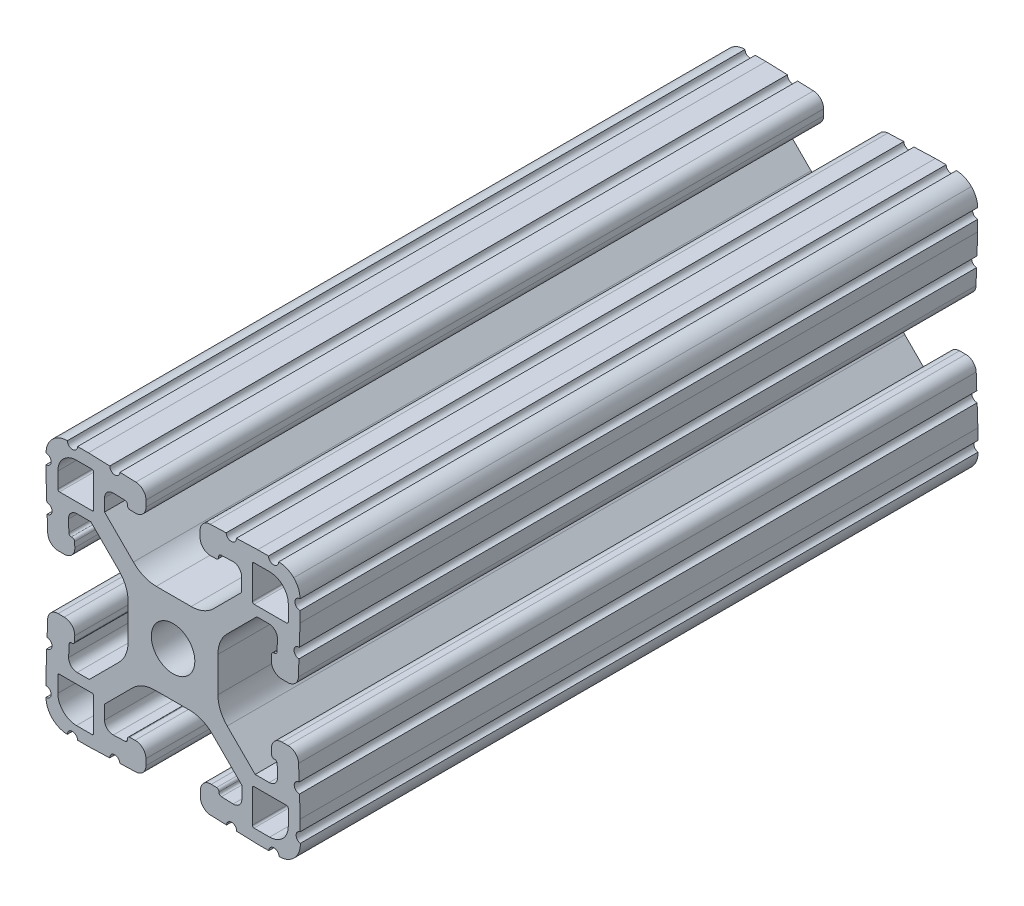
SolidWorks part; units mm, degrees
material "6061-T6 (SS)"
ref_plane "Front Plane" through (0, 0, 0) normal (0, 0, 1) x (1, 0, 0)
ref_plane "Top Plane" through (0, 0, 0) normal (0, 1, 0) x (1, 0, 0)
ref_plane "Right Plane" through (0, 0, 0) normal (1, 0, 0) x (0, 0, -1)
ref_plane "Plane1" through (0, 0, -25.4) normal (0, 0, -1) x (-1, 0, 0)
sketch "Sketch1" plane through (0, 0, -25.4) normal (0, 0, -1) x (-1, 0, 0)
  line L0 (-83.3577, 88.2941) -> (-83.3577, 93.1709)
  line L1 (-83.1037, 93.4249) -> (-80.767, 93.4249)
  line L2 (-77.9729, 90.6309) -> (-77.9729, 88.2941)
  line L3 (-78.2269, 88.0401) -> (-83.1037, 88.0401)
  line L4 (-83.3577, 59.2291) -> (-83.3577, 64.1059)
  line L5 (-83.1037, 64.3599) -> (-78.2269, 64.3599)
  line L6 (-77.9729, 64.1059) -> (-77.9729, 61.7691)
  line L7 (-80.767, 58.9751) -> (-83.1037, 58.9751)
  line L8 (-107.1423, 93.1709) -> (-107.1423, 88.2941)
  line L9 (-107.3963, 88.0401) -> (-112.2731, 88.0401)
  line L10 (-112.5271, 88.2941) -> (-112.5271, 90.6309)
  line L11 (-109.733, 93.4249) -> (-107.3963, 93.4249)
  line L12 (-107.1423, 64.1059) -> (-107.1423, 59.2291)
  line L13 (-107.3963, 58.9751) -> (-109.733, 58.9751)
  line L14 (-112.5271, 61.7691) -> (-112.5271, 64.1059)
  line L15 (-112.2731, 64.3599) -> (-107.3963, 64.3599)
  line L16 (-88.0437, 91.8626) -> (-86.2967, 91.9236)
  line L17 (-84.9824, 90.6544) -> (-84.9824, 88.8002)
  line L18 (-84.9824, 88.8002) -> (-89.3066, 84.476)
  line L19 (-92.7196, 83.0295) -> (-97.9616, 83.0295)
  line L20 (-101.3202, 84.4207) -> (-105.516, 88.6165)
  line L21 (-105.516, 88.6165) -> (-105.516, 90.7313)
  line L22 (-104.2017, 92.0006) -> (-102.4547, 91.9396)
  line L23 (-101.7262, 91.1059) -> (-100.9297, 91.0781)
  line L24 (-99.2999, 92.6519) -> (-99.2999, 93.5668)
  line L25 (-100.8197, 95.1407) -> (-103.2119, 95.2242)
  line L26 (-104.735, 95.2774) -> (-107.9359, 95.3892)
  line L27 (-107.9359, 95.3892) -> (-109.5615, 95.3892)
  line L28 (-114.2859, 90.6648) -> (-114.2859, 89.0392)
  line L29 (-114.2859, 89.0392) -> (-114.1741, 85.8383)
  line L30 (-114.1209, 84.3152) -> (-114.0374, 81.9231)
  line L31 (-112.4635, 80.4032) -> (-111.5486, 80.4032)
  line L32 (-109.9748, 82.033) -> (-110.0026, 82.8295)
  line L33 (-110.8377, 83.5577) -> (-110.8987, 85.3047)
  line L34 (-109.6294, 86.619) -> (-107.8072, 86.619)
  line L35 (-107.8072, 86.619) -> (-103.3649, 82.1768)
  line L36 (-101.9737, 78.8182) -> (-101.9737, 73.576)
  line L37 (-103.3649, 70.2174) -> (-107.5607, 66.0217)
  line L38 (-107.5607, 66.0217) -> (-109.6524, 66.0217)
  line L39 (-110.9217, 67.336) -> (-110.8607, 69.083)
  line L40 (-110.0322, 69.8124) -> (-110.0043, 70.6089)
  line L41 (-111.5782, 72.2387) -> (-112.4931, 72.2387)
  line L42 (-114.0669, 70.7189) -> (-114.1505, 68.3267)
  line L43 (-114.2036, 66.8036) -> (-114.3154, 63.6027)
  line L44 (-114.3154, 63.6027) -> (-114.3154, 61.9626)
  line L45 (-109.6111, 57.1437) -> (-107.9855, 57.1437)
  line L46 (-107.9855, 57.1437) -> (-104.7846, 57.2555)
  line L47 (-103.2615, 57.3086) -> (-100.8694, 57.3922)
  line L48 (-99.3495, 58.966) -> (-99.3495, 59.8809)
  line L49 (-100.9794, 61.4548) -> (-101.7758, 61.4269)
  line L50 (-102.5054, 60.599) -> (-104.2524, 60.538)
  line L51 (-105.5667, 61.8072) -> (-105.5667, 63.6295)
  line L52 (-105.5667, 63.6295) -> (-101.1311, 68.065)
  line L53 (-97.7725, 69.4562) -> (-92.5304, 69.4562)
  line L54 (-89.1717, 68.065) -> (-84.976, 63.8692)
  line L55 (-84.976, 63.8692) -> (-84.976, 61.7811)
  line L56 (-86.2903, 60.5118) -> (-88.0373, 60.5728)
  line L57 (-88.7596, 61.4332) -> (-89.5561, 61.461)
  line L58 (-91.1859, 59.8872) -> (-91.1859, 58.9723)
  line L59 (-89.6661, 57.3985) -> (-87.2739, 57.3149)
  line L60 (-85.7508, 57.2617) -> (-82.5499, 57.15)
  line L61 (-82.5499, 57.15) -> (-80.9244, 57.15)
  line L62 (-76.2, 61.8744) -> (-76.2, 63.4999)
  line L63 (-76.2, 63.4999) -> (-76.3117, 66.7008)
  line L64 (-76.3649, 68.2239) -> (-76.4484, 70.6161)
  line L65 (-78.0223, 72.1359) -> (-78.9372, 72.1359)
  line L66 (-80.511, 70.5061) -> (-80.4832, 69.7096)
  line L67 (-79.6552, 68.9801) -> (-79.5942, 67.2331)
  line L68 (-80.8634, 65.9188) -> (-82.6857, 65.9188)
  line L69 (-82.6857, 65.9188) -> (-87.1213, 70.3543)
  line L70 (-88.5125, 73.7128) -> (-88.5126, 78.955)
  line L71 (-87.1214, 82.3137) -> (-82.9257, 86.5095)
  line L72 (-82.9257, 86.5095) -> (-80.8375, 86.5095)
  line L73 (-79.5682, 85.1951) -> (-79.6293, 83.4482)
  line L74 (-80.4896, 82.7258) -> (-80.5175, 81.9294)
  line L75 (-78.9436, 80.2995) -> (-78.0287, 80.2995)
  line L76 (-76.4549, 81.8194) -> (-76.3713, 84.2115)
  line L77 (-76.3182, 85.7346) -> (-76.2064, 88.9355)
  line L78 (-76.2064, 88.9355) -> (-76.2064, 90.5611)
  line L79 (-80.9308, 95.2855) -> (-82.5564, 95.2855)
  line L80 (-82.5564, 95.2855) -> (-85.7573, 95.1737)
  line L81 (-87.2803, 95.1205) -> (-89.6725, 95.037)
  line L82 (-91.1924, 93.4632) -> (-91.1924, 92.5483)
  line L83 (-89.5625, 90.9744) -> (-88.7661, 91.0023)
  arc A0 (-83.3577, 93.1709) -> (-83.1037, 93.4249) centre (-83.1037, 93.1709) cw
  arc A1 (-80.767, 93.4249) -> (-77.9729, 90.6309) centre (-80.7669, 90.6309) cw
  arc A2 (-77.9729, 88.2941) -> (-78.2269, 88.0401) centre (-78.2269, 88.2941) cw
  arc A3 (-83.1037, 88.0401) -> (-83.3577, 88.2941) centre (-83.1037, 88.2941) cw
  arc A4 (-83.1037, 58.9751) -> (-83.3577, 59.2291) centre (-83.1037, 59.2291) cw
  arc A5 (-83.3577, 64.1059) -> (-83.1037, 64.3599) centre (-83.1037, 64.1059) cw
  arc A6 (-78.2269, 64.3599) -> (-77.9729, 64.1059) centre (-78.2269, 64.1059) cw
  arc A7 (-77.9729, 61.7691) -> (-80.767, 58.9751) centre (-80.7669, 61.7691) cw
  arc A8 (-107.3963, 93.4249) -> (-107.1423, 93.1709) centre (-107.3963, 93.1709) cw
  arc A9 (-107.1423, 88.2941) -> (-107.3963, 88.0401) centre (-107.3963, 88.2941) cw
  arc A10 (-112.2731, 88.0401) -> (-112.5271, 88.2941) centre (-112.2731, 88.2941) cw
  arc A11 (-112.5271, 90.6309) -> (-109.733, 93.4249) centre (-109.7331, 90.6309) cw
  arc A12 (-107.1423, 59.2291) -> (-107.3963, 58.9751) centre (-107.3963, 59.2291) cw
  arc A13 (-109.733, 58.9751) -> (-112.5271, 61.7691) centre (-109.7331, 61.7691) cw
  arc A14 (-112.5271, 64.1059) -> (-112.2731, 64.3599) centre (-112.2731, 64.1059) cw
  arc A15 (-107.3963, 64.3599) -> (-107.1423, 64.1059) centre (-107.3963, 64.1059) cw
  circle A16 centre (-95.25, 76.2) radius 3.2639
  arc A17 (-88.7661, 91.0023) -> (-88.3984, 91.383) centre (-88.7794, 91.383) ccw
  arc A18 (-88.3984, 91.383) -> (-88.0437, 91.8626) centre (-88.0304, 91.4819) cw
  arc A19 (-86.2967, 91.9236) -> (-84.9824, 90.6544) centre (-86.2524, 90.6544) cw
  arc A20 (-89.3066, 84.476) -> (-92.7196, 83.0295) centre (-92.7196, 87.7793) cw
  arc A21 (-97.9616, 83.0295) -> (-101.3202, 84.4207) centre (-97.9616, 87.7793) cw
  arc A22 (-105.516, 90.7313) -> (-104.2017, 92.0006) centre (-104.246, 90.7313) cw
  arc A23 (-102.4547, 91.9396) -> (-102.087, 91.5588) centre (-102.468, 91.5588) cw
  arc A24 (-102.087, 91.5588) -> (-101.7262, 91.1059) centre (-101.7129, 91.4867) ccw
  arc A25 (-100.9297, 91.0781) -> (-99.2999, 92.6519) centre (-100.8747, 92.6519) ccw
  arc A26 (-99.2999, 93.5668) -> (-100.8197, 95.1407) centre (-100.8747, 93.5668) ccw
  arc A27 (-103.2119, 95.2242) -> (-104.735, 95.2774) centre (-103.9735, 95.2508) cw
  arc A28 (-109.5615, 95.3892) -> (-111.0855, 95.3892) centre (-110.3235, 95.3892) cw
  arc A29 (-111.0855, 95.3892) -> (-113.3432, 94.4465) centre (-111.0855, 92.2142) ccw
  arc A30 (-113.3432, 94.4465) -> (-114.2859, 92.1888) centre (-111.1109, 92.1888) ccw
  arc A31 (-114.2859, 92.1888) -> (-114.2859, 90.6648) centre (-114.2859, 91.4268) cw
  arc A32 (-114.1741, 85.8383) -> (-114.1209, 84.3152) centre (-114.1475, 85.0768) cw
  arc A33 (-114.0374, 81.9231) -> (-112.4635, 80.4032) centre (-112.4635, 81.978) ccw
  arc A34 (-111.5486, 80.4032) -> (-109.9748, 82.033) centre (-111.5486, 81.978) ccw
  arc A35 (-110.0026, 82.8295) -> (-110.3834, 83.1972) centre (-110.3834, 82.8162) ccw
  arc A36 (-110.3834, 83.1972) -> (-110.8377, 83.5577) centre (-110.4569, 83.571) cw
  arc A37 (-110.8987, 85.3047) -> (-109.6294, 86.619) centre (-109.6294, 85.349) cw
  arc A38 (-103.3649, 82.1768) -> (-101.9737, 78.8182) centre (-106.7235, 78.8182) cw
  arc A39 (-101.9737, 73.576) -> (-103.3649, 70.2174) centre (-106.7235, 73.576) cw
  arc A40 (-109.6524, 66.0217) -> (-110.9217, 67.336) centre (-109.6524, 67.2917) cw
  arc A41 (-110.8607, 69.083) -> (-110.4799, 69.4507) centre (-110.4799, 69.0697) cw
  arc A42 (-110.4799, 69.4507) -> (-110.0322, 69.8124) centre (-110.413, 69.8257) ccw
  arc A43 (-110.0043, 70.6089) -> (-111.5782, 72.2387) centre (-111.5782, 70.6639) ccw
  arc A44 (-112.4931, 72.2387) -> (-114.0669, 70.7189) centre (-112.4931, 70.6639) ccw
  arc A45 (-114.1505, 68.3267) -> (-114.2036, 66.8036) centre (-114.1771, 67.5652) cw
  arc A46 (-114.3154, 61.9626) -> (-114.3332, 60.4644) centre (-114.4639, 61.2152) cw
  arc A47 (-114.3332, 60.4644) -> (-113.3928, 58.0864) centre (-111.1605, 60.3441) ccw
  arc A48 (-113.3928, 58.0864) -> (-111.1351, 57.1437) centre (-111.1351, 60.3187) ccw
  arc A49 (-111.1351, 57.1437) -> (-109.6111, 57.1437) centre (-110.3731, 57.1437) cw
  arc A50 (-104.7846, 57.2555) -> (-103.2615, 57.3086) centre (-104.0231, 57.2821) cw
  arc A51 (-100.8694, 57.3922) -> (-99.3495, 58.966) centre (-100.9243, 58.966) ccw
  arc A52 (-99.3495, 59.8809) -> (-100.9794, 61.4548) centre (-100.9243, 59.8809) ccw
  arc A53 (-101.7758, 61.4269) -> (-102.1435, 61.0462) centre (-101.7625, 61.0462) ccw
  arc A54 (-102.1435, 61.0462) -> (-102.5054, 60.599) centre (-102.5187, 60.9797) cw
  arc A55 (-104.2524, 60.538) -> (-105.5667, 61.8072) centre (-104.2967, 61.8072) cw
  arc A56 (-101.1311, 68.065) -> (-97.7725, 69.4562) centre (-97.7725, 64.7064) cw
  arc A57 (-92.5304, 69.4562) -> (-89.1717, 68.065) centre (-92.5304, 64.7064) cw
  arc A58 (-84.976, 61.7811) -> (-86.2903, 60.5118) centre (-86.246, 61.7811) cw
  arc A59 (-88.0373, 60.5728) -> (-88.405, 60.9536) centre (-88.024, 60.9536) cw
  arc A60 (-88.405, 60.9536) -> (-88.7596, 61.4332) centre (-88.7729, 61.0524) ccw
  arc A61 (-89.5561, 61.461) -> (-91.1859, 59.8872) centre (-89.6111, 59.8872) ccw
  arc A62 (-91.1859, 58.9723) -> (-89.6661, 57.3985) centre (-89.6111, 58.9723) ccw
  arc A63 (-87.2739, 57.3149) -> (-85.7508, 57.2617) centre (-86.5124, 57.2883) cw
  arc A64 (-80.9244, 57.15) -> (-79.4004, 57.15) centre (-80.1624, 57.15) cw
  arc A65 (-79.4004, 57.15) -> (-77.1426, 58.0927) centre (-79.4004, 60.325) ccw
  arc A66 (-77.1426, 58.0927) -> (-76.2, 60.3504) centre (-79.375, 60.3504) ccw
  arc A67 (-76.2, 60.3504) -> (-76.2, 61.8744) centre (-76.2, 61.1124) cw
  arc A68 (-76.3117, 66.7008) -> (-76.3649, 68.2239) centre (-76.3383, 67.4624) cw
  arc A69 (-76.4484, 70.6161) -> (-78.0223, 72.1359) centre (-78.0223, 70.5611) ccw
  arc A70 (-78.9372, 72.1359) -> (-80.511, 70.5061) centre (-78.9372, 70.5611) ccw
  arc A71 (-80.4832, 69.7096) -> (-80.1024, 69.342) centre (-80.1024, 69.723) ccw
  arc A72 (-80.1024, 69.342) -> (-79.6552, 68.9801) centre (-80.036, 68.9668) cw
  arc A73 (-79.5942, 67.2331) -> (-80.8634, 65.9188) centre (-80.8634, 67.1888) cw
  arc A74 (-87.1213, 70.3543) -> (-88.5125, 73.7128) centre (-83.7627, 73.7129) cw
  arc A75 (-88.5126, 78.955) -> (-87.1214, 82.3137) centre (-83.7628, 78.9551) cw
  arc A76 (-80.8375, 86.5095) -> (-79.5682, 85.1951) centre (-80.8375, 85.2395) cw
  arc A77 (-79.6293, 83.4482) -> (-80.01, 83.0805) centre (-80.01, 83.4615) cw
  arc A78 (-80.01, 83.0805) -> (-80.4896, 82.7258) centre (-80.1089, 82.7125) ccw
  arc A79 (-80.5175, 81.9294) -> (-78.9436, 80.2995) centre (-78.9436, 81.8743) ccw
  arc A80 (-78.0287, 80.2995) -> (-76.4549, 81.8194) centre (-78.0287, 81.8743) ccw
  arc A81 (-76.3713, 84.2115) -> (-76.3182, 85.7346) centre (-76.3448, 84.9731) cw
  arc A82 (-76.2064, 90.5611) -> (-76.2064, 92.0851) centre (-76.2064, 91.3231) cw
  arc A83 (-76.2064, 92.0851) -> (-77.1491, 94.3428) centre (-79.3814, 92.0851) ccw
  arc A84 (-77.1491, 94.3428) -> (-79.4068, 95.2855) centre (-79.4068, 92.1105) ccw
  arc A85 (-79.4068, 95.2855) -> (-80.9308, 95.2855) centre (-80.1688, 95.2855) cw
  arc A86 (-85.7573, 95.1737) -> (-87.2803, 95.1205) centre (-86.5188, 95.1471) cw
  arc A87 (-89.6725, 95.037) -> (-91.1924, 93.4632) centre (-89.6176, 93.4632) ccw
  arc A88 (-91.1924, 92.5483) -> (-89.5625, 90.9744) centre (-89.6176, 92.5483) ccw
extrude "Boss-Extrude1" add sketch "Sketch1" against normal blind 101.6
